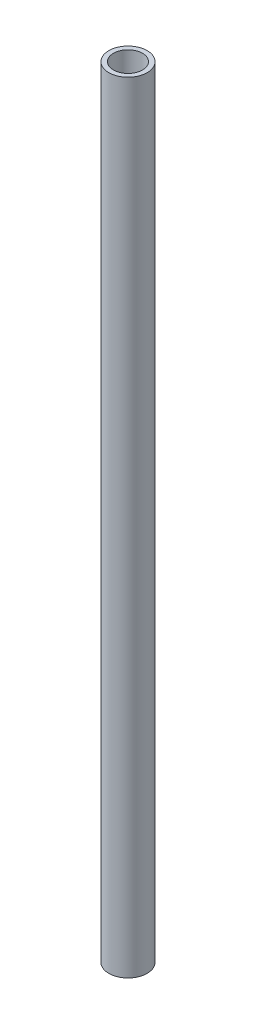
SolidWorks part; units mm, degrees
ref_plane "Front Plane" through (0, 0, 0) normal (0, 0, 1) x (1, 0, 0)
ref_plane "Top Plane" through (0, 0, 0) normal (0, 1, 0) x (1, 0, 0)
ref_plane "Right Plane" through (0, 0, 0) normal (1, 0, 0) x (0, 0, -1)
sketch "Sketch1" plane through (0, 0, 0) normal (0, 1, 0) x (1, 0, 0)
  circle A0 centre (0, 0) radius 13.5
  circle A1 centre (0, 0) radius 10.25
  dimension "D1" = 27
  dimension "D2" = 20.5
extrude "Boss-Extrude1" add sketch "Sketch1" along normal blind 550
